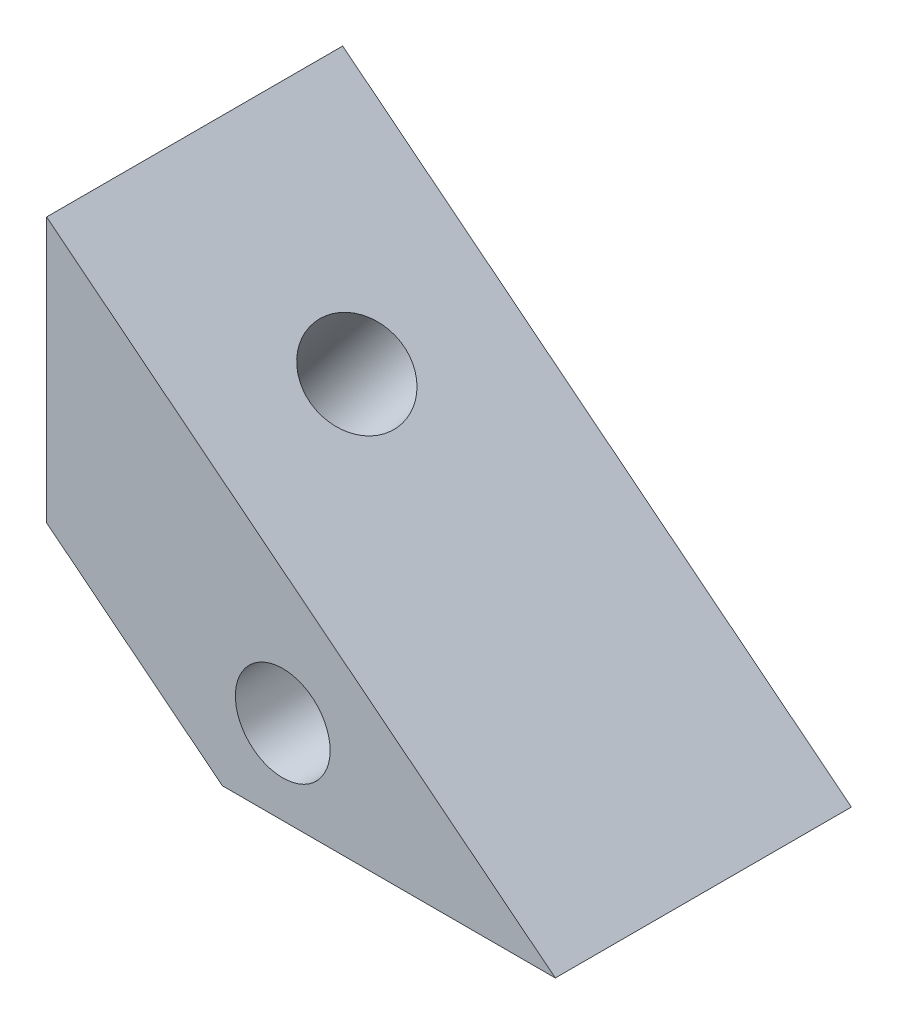
SolidWorks part; units mm, degrees
ref_plane "Alzado" through (0, 0, 0) normal (0, 0, 1) x (1, 0, 0)
ref_plane "Planta" through (0, 0, 0) normal (0, 1, 0) x (1, 0, 0)
ref_plane "Vista lateral" through (0, 0, 0) normal (1, 0, 0) x (0, 0, -1)
sketch "Croquis1" plane through (0, 0, 0) normal (0, 0, 1) x (1, 0, 0)
  line L0 (0, 0) -> (22, 0) construction
  line L1 (22, 0) -> (0, 17.5) construction
  line L2 (0, 17.5) -> (0, 0) construction
  line L3 (17.1809, 0) -> (0, 13.6666) construction
  line L4 (17.1809, 0) -> (5.9364, 0)
  line L5 (5.9364, 0) -> (0, 4.7221)
  line L6 (0, 4.7221) -> (0, 13.6666)
  line L7 (0, 13.6666) -> (17.1809, 0)
  line L8 (0, 0) -> (8.5258, 10.7181) construction
  line L9 (0, 9.1944) -> (11.5586, 0) construction
  circle A0 centre (7.9758, 2.85) radius 1.6
  dimension "D5" = 3.2
  dimension "D1" = 17.5
  dimension "D2" = 22
  dimension "D3" = 3
  dimension "D4" = 7
  dimension "D6" = 2.85
extrude "Saliente-Extruir1" add sketch "Croquis1" along normal blind 10
sketch "Croquis2" plane through (0, 0, 10) normal (0, 0, 1) x (1, 0, 0)
  line L1 (6.3303, 0) -> (9.6212, 0)
  line L2 (9.6212, 0) -> (11.2667, 2.85)
  line L3 (11.2667, 2.85) -> (9.6212, 5.7)
  line L4 (9.6212, 5.7) -> (6.3303, 5.7)
  line L5 (6.3303, 5.7) -> (4.6849, 2.85)
  line L6 (4.6849, 2.85) -> (6.3303, 0)
  line L7 (5.9364, 0) -> (17.1809, 0) construction
  circle A0 centre (7.9758, 2.85) radius 2.85 construction
  dimension "D1" = 5.7
extrude "Cortar-Extruir1" cut sketch "Croquis2" against normal offset from surface (5.5 mm away) 4.5 up to face at (5.7793, 4.5972, 0)
sketch "Croquis3" plane through (6.6582, 8.3703, 0) normal (0.6225, 0.7826, 0) x (0.7826, -0.6225, 0)
  line L0 (-8.5078, -5) -> (13.4458, -5) construction
  line L1 (-8.5078, -10) -> (-8.5078, 0) construction
  line L2 (13.4458, -10) -> (13.4458, 0) construction
  circle A0 centre (-1.5078, -5) radius 1.6
  dimension "D1" = 3.2
  dimension "D2" = 7
extrude "Cortar-Extruir2" cut sketch "Croquis3" against normal up to next
sketch "Croquis4" plane through (2.3005, 2.8921, 0) normal (-0.6225, -0.7826, 0) x (0.7826, -0.6225, 0)
  line L1 (1.7831, 5) -> (0.1376, 7.85)
  line L2 (0.1376, 7.85) -> (-3.1532, 7.85)
  line L3 (-3.1532, 7.85) -> (-4.7987, 5)
  line L4 (-4.7987, 5) -> (-3.1532, 2.15)
  line L5 (-3.1532, 2.15) -> (0.1376, 2.15)
  line L6 (0.1376, 2.15) -> (1.7831, 5)
  circle A0 centre (-1.5078, 5) radius 2.85 construction
  dimension "D1" = 5.7
extrude "Cortar-Extruir3" cut sketch "Croquis4" against normal offset from surface (2.5 mm away) 4.5 up to face at (4.226, 10.305, 5)
mirror "Simetría1" about plane through (0, 13.6666, 0) normal (0, 0, 1) of bodies 104
delete or keep bodies "Sólido-Eliminar1" type delete bodies bodies 104
